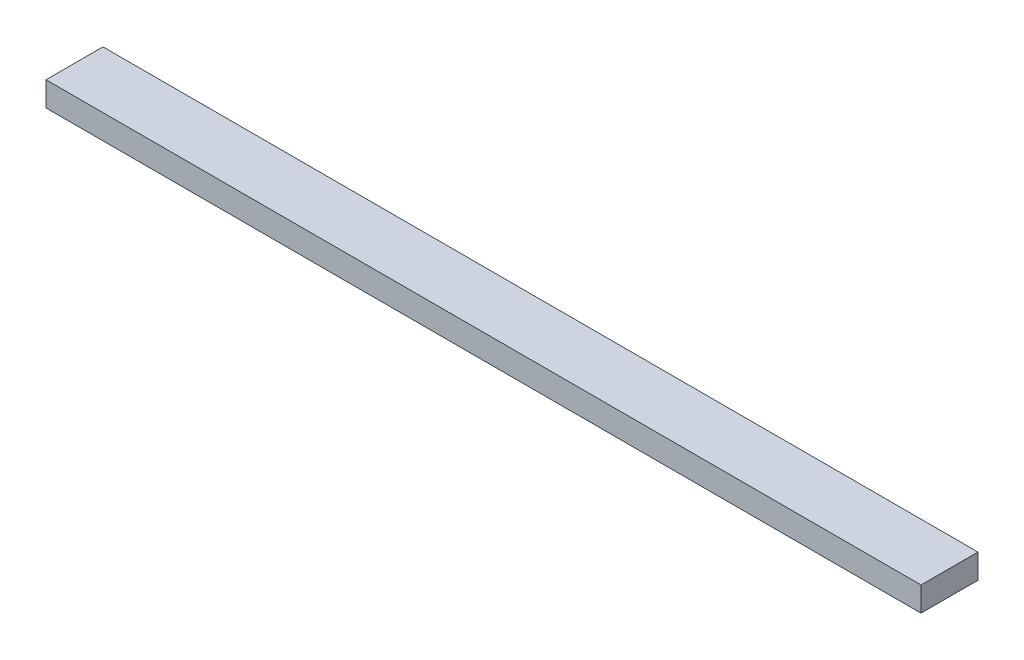
SolidWorks part; units mm, degrees
material "Pine"
ref_plane "Front Plane" through (0, 0, 0) normal (0, 0, 1) x (1, 0, 0)
ref_plane "Top Plane" through (0, 0, 0) normal (0, 1, 0) x (1, 0, 0)
ref_plane "Right Plane" through (0, 0, 0) normal (1, 0, 0) x (0, 0, -1)
sketch "Sketch1" plane through (0, 0, 0) normal (0, 1, 0) x (1, 0, 0)
  line L1 (0, 0) -> (1365.2754, 0)
  line L2 (0, 0) -> (0, 88.9)
  line L3 (0, 88.9) -> (1365.2754, 88.9)
  line L4 (1365.2754, 0) -> (1365.2754, 88.9)
  dimension "D1" = 88.9
  dimension "D2" = 1365.2754
extrude "Boss-Extrude1" add sketch "Sketch1" along normal blind 38.1
